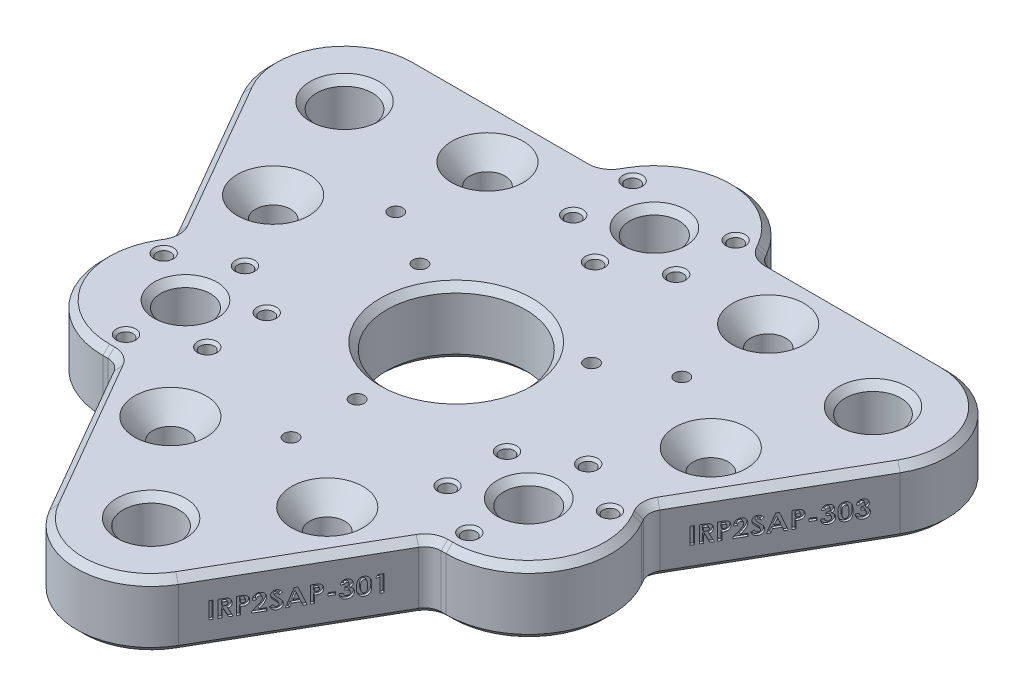
SolidWorks part; units mm, degrees
material "6061-T6 (SS)"
ref_plane "Front" through (0, 0, 0) normal (0, 0, 1) x (1, 0, 0)
ref_plane "Top" through (0, 0, 0) normal (0, 1, 0) x (1, 0, 0)
ref_plane "Right" through (0, 0, 0) normal (1, 0, 0) x (0, 0, -1)
sketch "Sketch1" plane through (0, 0, 0) normal (0, 1, 0) x (1, 0, 0)
  line L0 (-50.8, 43.6169) -> (50.8, 43.6169)
  line L1 (0, 43.6169) -> (0, 0) construction
  line L2 (63.1733, 22.1856) -> (12.3733, -65.8025)
  line L3 (0, 0) -> (-37.7733, -21.8084) construction
  line L4 (-12.3733, -65.8025) -> (-63.1733, 22.1856)
  line L5 (-37.7733, -21.8084) -> (37.7733, -21.8084) construction
  line L6 (37.7733, -21.8084) -> (0, 0) construction
  arc A0 (-50.8, 43.6169) -> (-63.1733, 22.1856) centre (-50.8, 29.3294) ccw
  arc A1 (63.1733, 22.1856) -> (50.8, 43.6169) centre (50.8, 29.3294) ccw
  arc A2 (-12.3733, -65.8025) -> (12.3733, -65.8025) centre (0, -58.6588) ccw
  dimension "D2" = 28.575
  dimension "D1" = 101.6
extrude "Boss-Extrude1" add sketch "Sketch1" along normal blind 12.7
hole_wizard "1/2-13 Tapped Hole1" positions "Sketch2" profile "Sketch3" tap size "1/2-13" standard "ANSI Inch" end condition through all
sketch "Sketch2" plane through (0, 12.7, 0) normal (0, 1, 0) x (1, 0, 0)
  point P0 (-50.8, 29.3294)
  point P3 (0, -58.6588)
  point P6 (50.8, 29.3294)
sketch "Sketch3" plane through (-50.8, 12.7, -29.3294) normal (1, 0, 0) x (0, 0, 1)
  line L0 (0, 0) -> (0, 12.7)
  line L1 (0, 12.7) -> (5.3581, 12.7)
  line L2 (5.3581, 12.7) -> (5.3581, 0)
  line L5 (5.3581, 0) -> (0, 0)
  line L11 (0, -6.35) -> (0, 107.95) construction
  dimension "Thru Tap Drill Dia." = 10.7163
  dimension "Thru Tap Drill Depth" = 12.7
cosmetic thread "Hole Thread1" parameters "D2"=12.7
cosmetic thread "Hole Thread2" parameters "D2"=12.7
cosmetic thread "Hole Thread3" parameters "D2"=12.7
sketch "Sketch6" plane through (0, 12.7, 0) normal (0, 1, 0) x (1, 0, 0)
  line L3 (-15.1457, 43.6169) -> (-13.7482, 46.0375)
  line L4 (50.8, 43.6169) -> (-50.8, 43.6169) construction
  line L5 (13.7482, 46.0375) -> (15.1457, 43.6169)
  line L6 (15.1457, 43.6169) -> (-15.1457, 43.6169)
  line L7 (0, 38.1) -> (0, 0) construction
  line L14 (32.9956, -34.925) -> (30.2005, -34.925)
  line L15 (45.3462, -8.6919) -> (46.7437, -11.1125)
  line L16 (-46.7437, -11.1125) -> (-45.3462, -8.6919)
  line L17 (-30.2005, -34.925) -> (-32.9956, -34.925)
  line L18 (-45.3462, -8.6919) -> (-30.2005, -34.925)
  line L19 (45.3462, -8.6919) -> (30.2005, -34.925)
  line L20 (12.3733, -65.8025) -> (63.1733, 22.1856) construction
  line L21 (-63.1733, 22.1856) -> (-12.3733, -65.8025) construction
  arc A3 (-13.7482, 46.0375) -> (13.7482, 46.0375) centre (0, 38.1) cw
  arc A6 (46.7437, -11.1125) -> (32.9956, -34.925) centre (32.9956, -19.05) cw
  arc A7 (-32.9956, -34.925) -> (-46.7437, -11.1125) centre (-32.9956, -19.05) cw
  point P21 (0, 0)
  dimension "D1" = 15.875
  dimension "D2" = 60
  dimension "D4" = 38.1
  dimension "D3" = 3
extrude "Boss-Extrude2" add sketch "Sketch6" against normal blind 12.7
fillet "Fillet1" radius 3.175 6 edges at (30.2005, 6.35, 34.925) (45.3462, 6.35, 8.6919) (15.1457, 6.35, -43.6169) (-15.1457, 6.35, -43.6169) (-30.2005, 6.35, 34.925) (-45.3462, 6.35, 8.6919)
chamfer "Chamfer1" distance 1.27 angle 45 54 edges at (63.1733, 0, -36.4731) (33.8894, 0, -43.6169) (-33.8894, 0, -43.6169) (-63.1733, 0, -36.4731) (-54.718, 0, -7.5406) (-20.8286, 0, 51.1575) (0, 0, 72.9463) (20.8286, 0, 51.1575) (54.718, 0, -7.5406) (50.8, 0, -23.9713) (0, 0, 64.0169) (-50.8, 0, -23.9713) (50.8, 12.7, -23.9713) (0, 12.7, 64.0169) (-50.8, 12.7, -23.9713) (0, 12.7, 72.9463) (-20.8286, 12.7, 51.1575) (-54.718, 12.7, -7.5406) (-63.1733, 12.7, -36.4731) (-33.8894, 12.7, -43.6169) (33.8894, 12.7, -43.6169) (63.1733, 12.7, -36.4731) (54.718, 12.7, -7.5406) (20.8286, 12.7, 51.1575) (0, 12.7, -53.975) (0, 0, -53.975) (13.9887, 12.7, -45.6209) (13.9887, 0, -45.6209) (15.3913, 12.7, -44.0423) (45.8374, 12.7, 8.6919) (46.5032, 0, 10.6959) (46.5032, 12.7, 10.6959) (46.7437, 12.7, 26.9875) (46.7437, 0, 26.9875) (32.5146, 12.7, 34.925) (32.5146, 0, 34.925) (30.4461, 12.7, 35.3504) (-30.4461, 12.7, 35.3504) (-32.5146, 0, 34.925) (-32.5146, 12.7, 34.925) (-46.7437, 12.7, 26.9875) (-46.7437, 0, 26.9875) (-46.5032, 12.7, 10.6959) (-46.5032, 0, 10.6959) (-45.8374, 12.7, 8.6919) (-15.3913, 12.7, -44.0423) (-13.9887, 0, -45.6209) (-13.9887, 12.7, -45.6209) (-15.3913, 0, -44.0423) (-45.8374, 0, 8.6919) (-30.4461, 0, 35.3504) (30.4461, 0, 35.3504) (45.8374, 0, 8.6919) (15.3913, 0, -44.0423)
hole_wizard "#4-40 Tapped Hole1" positions "Sketch7" profile "Sketch8" tap size "#4-40" standard "ANSI Inch"
sketch "Sketch7" plane through (-37.7733, 0, 21.8084) normal (-0.866, 0, 0.5) x (0.5, 0, 0.866)
  line L0 (-50.8, 6.35) -> (-44.45, 6.35) construction
  line L1 (-50.8, 11.43) -> (-50.8, 1.27) construction
  line L2 (-44.45, 6.35) -> (0, 6.35) construction
  line L8 (44.45, 6.35) -> (50.8, 6.35) construction
  line L9 (50.8, 11.43) -> (50.8, 1.27) construction
  line L13 (0, 6.35) -> (44.45, 6.35) construction
  line L15 (12.6483, 12.7) -> (-12.6483, 12.7) construction
  point P0 (-44.45, 6.35)
  point P2 (44.45, 6.35)
  point P41 (0, 12.7)
  dimension "D1" = 44.45
sketch "Sketch8" plane through (-59.9983, 6.35, -16.6864) normal (0, 1, 0) x (0.5, 0, 0.866)
  line L0 (0, 0) -> (0, 8.6167)
  line L1 (0, 8.6167) -> (1.1303, 7.9375)
  line L2 (1.1303, 7.9375) -> (1.1303, 0)
  line L5 (1.1303, 0) -> (0, 0)
  line L10 (0, 8.6167) -> (-1.1303, 7.9375) construction
  line L11 (0, -6.35) -> (0, 107.95) construction
  dimension "Tap Drill Dia." = 2.2606
  dimension "Tap Drill Depth" = 7.9375
  dimension "Drill Angle" = 118
cosmetic thread "Hole Thread4" parameters "D1"=6.35, "D2"=2.8448
cosmetic thread "Hole Thread5" parameters "D1"=6.35, "D2"=2.8448
ref_plane "Plane1" through (0, 0, 0) normal (-0.5, 0, 0.866) x (0.866, 0, 0.5)
mirror "Mirror1" about plane through (0, 0, 0) normal (-0.5, 0, 0.866) of "#4-40 Tapped Hole1"
cosmetic thread "Hole Thread6" parameters "D1"=6.35, "D2"=2.8448
cosmetic thread "Hole Thread7" parameters "D1"=6.35, "D2"=2.8448
hole_wizard "#6-32 Tapped Hole2" positions "Sketch9" profile "Sketch10" tap size "#6-32" standard "ANSI Inch" end condition through all
sketch "Sketch9" plane through (0, 12.7, 0) normal (0, 1, 0) x (1, 0, 0)
  line L1 (0, 49.53) -> (-9.8987, 43.815) construction
  line L2 (-9.8987, 43.815) -> (-9.8987, 32.385) construction
  line L3 (-9.8987, 32.385) -> (0, 26.67) construction
  line L4 (0, 26.67) -> (9.8987, 32.385) construction
  line L5 (9.8987, 32.385) -> (9.8987, 43.815) construction
  line L6 (9.8987, 43.815) -> (0, 49.53) construction
  line L8 (42.8942, -24.765) -> (42.8942, -13.335) construction
  line L9 (42.8942, -13.335) -> (32.9956, -7.62) construction
  line L10 (32.9956, -7.62) -> (23.0969, -13.335) construction
  line L11 (23.0969, -13.335) -> (23.0969, -24.765) construction
  line L12 (23.0969, -24.765) -> (32.9956, -30.48) construction
  line L13 (32.9956, -30.48) -> (42.8942, -24.765) construction
  line L15 (-42.8942, -24.765) -> (-32.9956, -30.48) construction
  line L16 (-32.9956, -30.48) -> (-23.0969, -24.765) construction
  line L17 (-23.0969, -24.765) -> (-23.0969, -13.335) construction
  line L18 (-23.0969, -13.335) -> (-32.9956, -7.62) construction
  line L19 (-32.9956, -7.62) -> (-42.8942, -13.335) construction
  line L20 (-42.8942, -13.335) -> (-42.8942, -24.765) construction
  line L21 (-32.9956, -19.05) -> (-23.0969, -13.335) construction
  line L24 (32.9956, -19.05) -> (23.0969, -13.335) construction
  line L26 (-23.0969, -13.335) -> (0, 0) construction
  line L27 (0, 0) -> (23.0969, -13.335) construction
  line L28 (0, 0) -> (0, -19.05) construction
  line L29 (0, -19.05) -> (0, -31.75) construction
  line L31 (0, 0) -> (16.4978, 9.525) construction
  line L32 (16.4978, 9.525) -> (27.4963, 15.875) construction
  line L34 (0, 0) -> (-16.4978, 9.525) construction
  line L35 (-16.4978, 9.525) -> (-27.4963, 15.875) construction
  circle A1 centre (0, 38.1) radius 9.8987 construction
  circle A2 centre (32.9956, -19.05) radius 9.8987 construction
  circle A3 centre (-32.9956, -19.05) radius 9.8987 construction
  circle A4 centre (0, 38.1) radius 11.43 construction
  point P6 (-9.8987, 43.815)
  point P7 (-9.8987, 32.385)
  point P8 (0, 26.67)
  point P9 (9.8987, 32.385)
  point P10 (9.8987, 43.815)
  point P16 (42.8942, -13.335)
  point P17 (32.9956, -7.62)
  point P18 (23.0969, -13.335)
  point P19 (23.0969, -24.765)
  point P20 (32.9956, -30.48)
  point P26 (-32.9956, -30.48)
  point P27 (-23.0969, -24.765)
  point P28 (-23.0969, -13.335)
  point P29 (-32.9956, -7.62)
  point P30 (-42.8942, -13.335)
  point P93 (0, -19.05)
  point P94 (0, -31.75)
  point P99 (16.4978, 9.525)
  point P100 (27.4963, 15.875)
  point P103 (-16.4978, 9.525)
  point P104 (-27.4963, 15.875)
  dimension "D1" = 22.86
  dimension "D2" = 19.05
  dimension "D3" = 12.7
sketch "Sketch10" plane through (-27.4963, 12.7, -15.875) normal (1, 0, 0) x (0, 0, 1)
  line L0 (0, 0) -> (0, 12.7)
  line L1 (0, 12.7) -> (1.3525, 12.7)
  line L2 (1.3525, 12.7) -> (1.3525, 0)
  line L5 (1.3525, 0) -> (0, 0)
  line L11 (0, -6.35) -> (0, 107.95) construction
  dimension "Thru Tap Drill Dia." = 2.7051
  dimension "Thru Tap Drill Depth" = 12.7
cosmetic thread "Hole Thread8" parameters "D2"=3.5052
cosmetic thread "Hole Thread9" parameters "D2"=3.5052
cosmetic thread "Hole Thread10" parameters "D2"=3.5052
cosmetic thread "Hole Thread11" parameters "D2"=3.5052
cosmetic thread "Hole Thread12" parameters "D2"=3.5052
cosmetic thread "Hole Thread13" parameters "D2"=3.5052
cosmetic thread "Hole Thread14" parameters "D2"=3.5052
cosmetic thread "Hole Thread15" parameters "D2"=3.5052
cosmetic thread "Hole Thread16" parameters "D2"=3.5052
cosmetic thread "Hole Thread23" parameters "D2"=3.5052
cosmetic thread "Hole Thread24" parameters "D2"=3.5052
cosmetic thread "Hole Thread25" parameters "D2"=3.5052
cosmetic thread "Hole Thread26" parameters "D2"=3.5052
cosmetic thread "Hole Thread27" parameters "D2"=3.5052
cosmetic thread "Hole Thread28" parameters "D2"=3.5052
cosmetic thread "Hole Thread29" parameters "D2"=3.5052
cosmetic thread "Hole Thread30" parameters "D2"=3.5052
cosmetic thread "Hole Thread31" parameters "D2"=3.5052
cosmetic thread "Hole Thread32" parameters "D2"=3.5052
cosmetic thread "Hole Thread33" parameters "D2"=3.5052
cosmetic thread "Hole Thread34" parameters "D2"=3.5052
sketch "Sketch11" plane through (0, 12.7, 0) normal (0, 1, 0) x (1, 0, 0)
  circle A0 centre (0, 0) radius 13.335
  dimension "D1" = 26.67
extrude "Cut-Extrude1" cut sketch "Sketch11" against normal through all
hole_wizard "CSK for 1/4 Flat Head Machine Screw1" positions "Sketch12" profile "Sketch13" countersink size "1/4" standard "ANSI Inch" end condition through all
sketch "Sketch12" plane through (0, 12.7, 0) normal (0, 1, 0) x (1, 0, 0)
  line L0 (-26.9875, 32.9956) -> (-42.0687, 6.8741) construction
  line L1 (-42.0687, 6.8741) -> (-15.0812, -39.8696) construction
  line L2 (-15.0812, -39.8696) -> (15.0813, -39.8696) construction
  line L3 (15.0813, -39.8696) -> (42.0687, 6.8741) construction
  line L4 (42.0687, 6.8741) -> (26.9875, 32.9956) construction
  line L5 (26.9875, 32.9956) -> (-26.9875, 32.9956) construction
  line L6 (0, 32.9956) -> (0, 0) construction
  line L7 (0, 0) -> (0, -39.8696) construction
  line L9 (-34.5281, 19.9348) -> (0, 0) construction
  line L10 (0, 0) -> (34.5281, 19.9348) construction
  line L18 (-42.0687, 6.8741) -> (-57.15, 32.9956) construction
  line L19 (-57.15, 32.9956) -> (-26.9875, 32.9956) construction
  line L21 (26.9875, 32.9956) -> (57.15, 32.9956) construction
  line L22 (57.15, 32.9956) -> (42.0687, 6.8741) construction
  line L24 (-15.0812, -39.8696) -> (0, -65.9911) construction
  line L25 (0, -65.9911) -> (15.0813, -39.8696) construction
  point P0 (-15.0812, -39.8696)
  point P2 (15.0813, -39.8696)
  point P4 (42.0687, 6.8741)
  point P6 (26.9875, 32.9956)
  point P8 (-26.9875, 32.9956)
  point P10 (-42.0687, 6.8741)
  dimension "D1" = 114.3
  dimension "D2" = 53.975
sketch "Sketch13" plane through (-15.0812, 12.7, 39.8696) normal (1, 0, 0) x (0, 0, 1)
  line L0 (0, 0) -> (0, 12.7)
  line L1 (0, 12.7) -> (3.3782, 12.7)
  line L2 (3.3782, 12.7) -> (3.3782, 4.0289)
  line L3 (3.3782, 4.0289) -> (6.8805, 0)
  line L5 (6.8805, 0) -> (0, 0)
  line L6 (-3.3782, 4.0289) -> (-6.8805, 0) construction
  line L11 (0, -6.35) -> (0, 107.95) construction
  dimension "Thru Hole Dia." = 6.7564
  dimension "Thru Hole Depth" = 12.7
  dimension "Near C'Sink Dia." = 13.761
  dimension "Near C'Sink Angle" = 82
sketch "Sketch14" plane through (0, 0, 0) normal (0, -1, 0) x (-1, 0, 0)
  circle A0 centre (32.9956, -19.05) radius 4.7625
  circle A1 centre (-32.9956, -19.05) radius 4.7625
  circle A2 centre (0, 38.1) radius 4.7625
  arc A3 (12.6483, 45.4025) -> (-12.6483, 45.4025) centre (0, 38.1) ccw construction
  arc A4 (-45.6439, -11.7475) -> (-32.9956, -33.655) centre (-32.9956, -19.05) ccw construction
  arc A5 (32.9956, -33.655) -> (45.6439, -11.7475) centre (32.9956, -19.05) ccw construction
  dimension "D1" = 9.525
extrude "Cut-Extrude2" cut sketch "Sketch14" against normal through all
chamfer "Chamfer3" distance 0.508 angle 45 30 edges at (9.8987, 12.7, -42.4625) (9.8987, 0, -42.4625) (-9.8987, 12.7, -42.4624) (-9.8987, 0, -42.4624) (-9.8987, 12.7, -31.0325) (-9.8987, 0, -31.0325) (9.8987, 12.7, -31.0325) (9.8987, 0, -31.0325) (0, 12.7, -25.3175) (0, 0, -25.3175) (32.9956, 12.7, 8.9725) (32.9956, 0, 8.9725) (42.8942, 12.7, 14.6875) (42.8942, 0, 14.6875) (32.9956, 12.7, 31.8325) (32.9956, 0, 31.8325) (23.0969, 12.7, 26.1176) (23.0969, 0, 26.1176) (23.0969, 12.7, 14.6875) (23.0969, 0, 14.6875) (-23.0969, 12.7, 14.6876) (-23.0969, 0, 14.6876) (-32.9956, 12.7, 8.9726) (-32.9956, 0, 8.9726) (-23.0969, 12.7, 26.1176) (-23.0969, 0, 26.1176) (-32.9956, 12.7, 31.8326) (-32.9956, 0, 31.8326) (-42.8942, 12.7, 14.6876) (-42.8942, 0, 14.6876)
chamfer "Chamfer2" distance 1.27 angle 45 14 edges at (0, 12.7, 13.335) (0, 0, 13.335) (-32.9956, 0, 14.2875) (-32.9956, 12.7, 14.2875) (32.9956, 0, 14.2875) (32.9956, 12.7, 14.2875) (0, 0, -42.8625) (0, 12.7, -42.8625) (-42.0687, 0, -3.4959) (-26.9875, 0, -29.6174) (26.9875, 0, -29.6174) (42.0687, 0, -3.4959) (15.0813, 0, 43.2478) (-15.0812, 0, 43.2478)
sketch "Sketch16" plane through (37.7733, 0, 21.8084) normal (0.866, 0, 0.5) x (0.5, 0, -0.866)
  line L0 (-50.8, 4.7625) -> (-16.9788, 4.7625) construction
  line L1 (-50.8, 11.43) -> (-50.8, 1.27) construction
  line L2 (-16.9788, 1.27) -> (-16.9788, 11.43) construction
  line L3 (-33.8894, 1.27) -> (-33.8894, 4.7625) construction
  line L4 (-50.8, 1.27) -> (-16.9788, 1.27) construction
  line L5 (-33.8894, 4.7625) -> (-33.8894, 7.9375) construction
  line L6 (-33.8894, 7.9375) -> (-33.8894, 11.43) construction
  line L7 (-16.9788, 11.43) -> (-50.8, 11.43) construction
  line L8 (0, 0) -> (0, 11.43) construction
  line L9 (13.7482, 11.43) -> (-13.7482, 11.43) construction
  line L10 (50.8, 4.7625) -> (16.9788, 4.7625) construction
  text T0 "<b>IRP2SAP-301</b>"
  text T1 "<b>IRP2SAP-303</b>"
  dimension "D1" = 3.175
extrude "Cut-Extrude3" cut sketch "Sketch16" against normal blind 0.508
